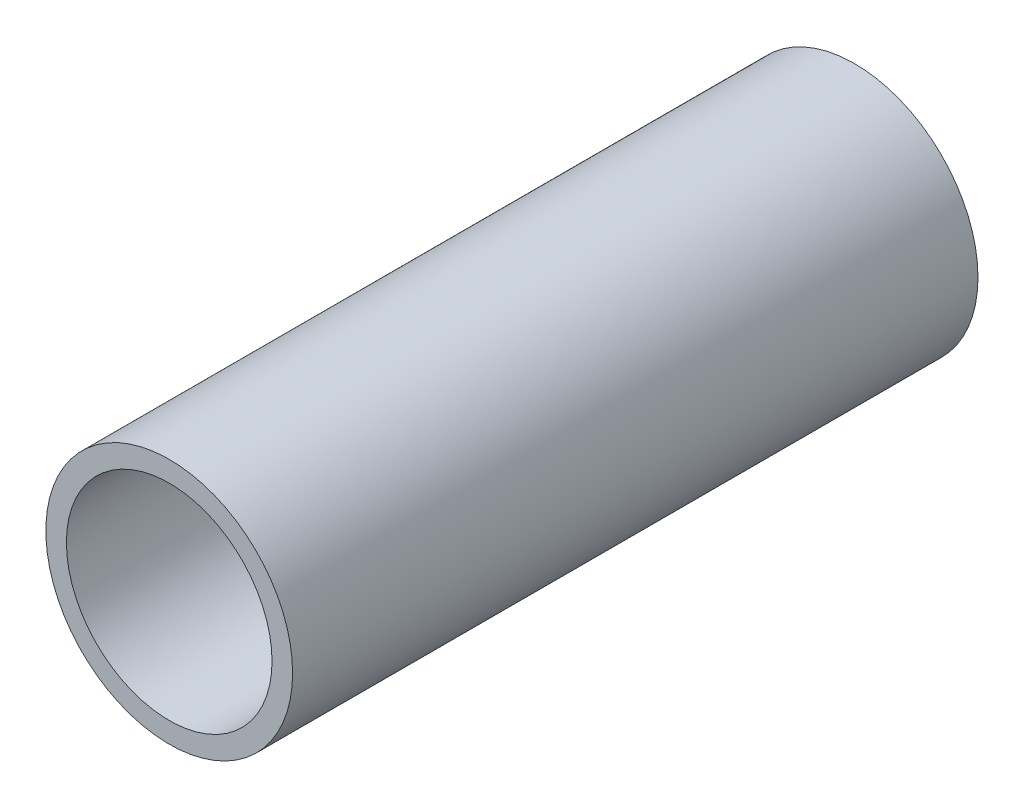
SolidWorks part; units mm, degrees
ref_plane "Front Plane" through (0, 0, 0) normal (0, 0, 1) x (1, 0, 0)
ref_plane "Top Plane" through (0, 0, 0) normal (0, 1, 0) x (1, 0, 0)
ref_plane "Right Plane" through (0, 0, 0) normal (1, 0, 0) x (0, 0, -1)
sketch "Sketch1" plane through (0, 0, 0) normal (0, 0, 1) x (1, 0, 0)
  circle A0 centre (0, 0) radius 15
  circle A1 centre (0, 0) radius 18
  dimension "D1" = 36
  dimension "D2" = 30
extrude "Boss-Extrude1" add sketch "Sketch1" along normal blind 100
